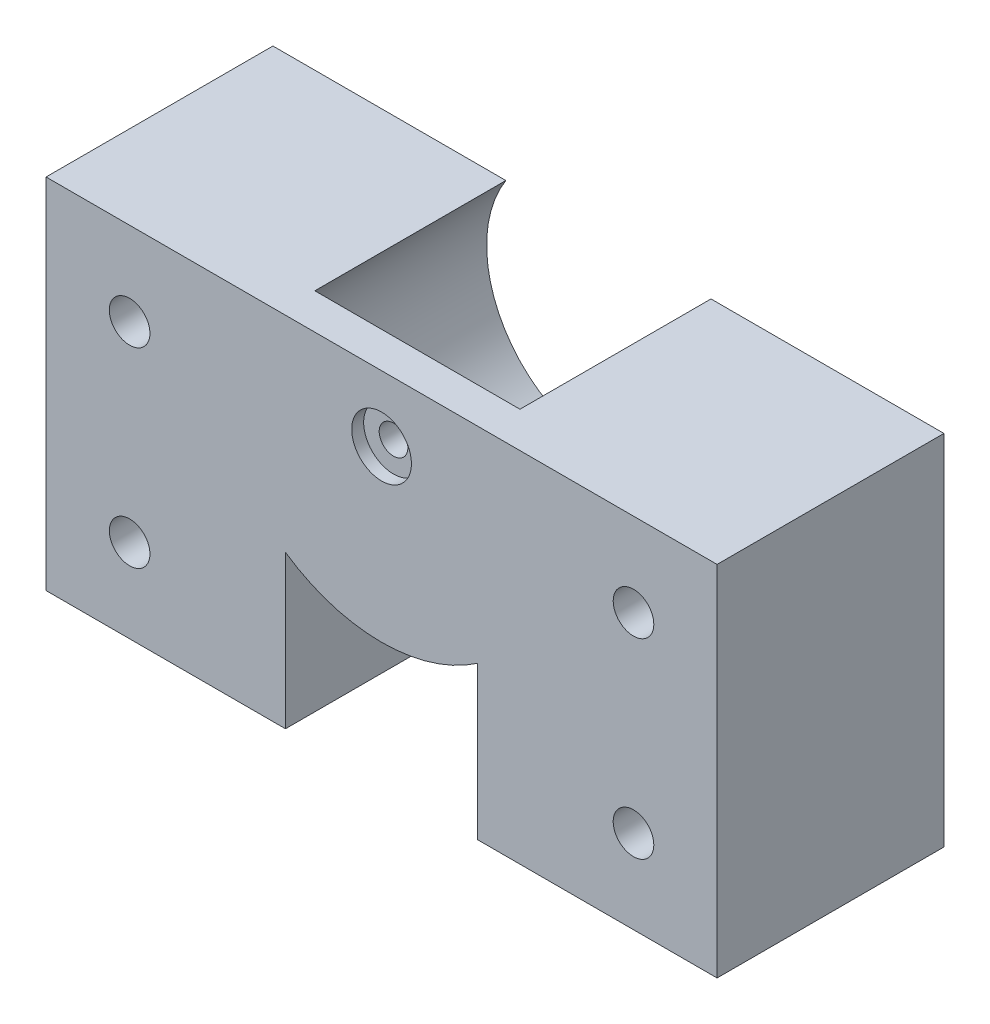
SolidWorks part; units mm, degrees
ref_plane "Front Plane" through (0, 0, 0) normal (0, 0, 1) x (1, 0, 0)
ref_plane "Top Plane" through (0, 0, 0) normal (0, 1, 0) x (1, 0, 0)
ref_plane "Right Plane" through (0, 0, 0) normal (1, 0, 0) x (0, 0, -1)
sketch "Sketch1" plane through (0, 0, 0) normal (0, 0, 1) x (1, 0, 0)
  line L0 (19.5099, 0) -> (0, 0)
  line L1 (28.1, -5.5) -> (28.1, -10) construction
  line L2 (0, 0) -> (0, -30)
  line L3 (0, -30) -> (56.2, -30)
  line L4 (36.6901, 0) -> (56.2, 0)
  line L5 (56.2, 0) -> (56.2, -30)
  line L6 (19.5099, 0) -> (36.6901, 0) construction
  line L7 (35.8259, 0) -> (36.6901, 0)
  line L8 (35.8259, -3) -> (37.9889, -3)
  line L18 (0, -15) -> (56.2, -15) construction
  arc A0 (19.5099, 0) -> (37.9889, -3) centre (28.1, -5.5) ccw
  arc A1 (35.8259, 0) -> (35.8259, -3) centre (35.8259, -1.5) ccw
  dimension "D4" = 30
  dimension "D5" = 1.5
  dimension "D2" = 5.5
  dimension "D1" = 10.2
  dimension "D3" = 56.2
extrude "Boss-Extrude1" add sketch "Sketch1" along normal blind 16
sketch "Sketch2" [suppressed] plane through (0, 0, 0) normal (0, 0, -1) x (-1, 0, 0)
  line L0 (-56.2, -15) -> (0, -15) construction
  line L1 (-56.2, -30) -> (-56.2, 0) construction
  line L2 (-46.0015, -7) -> (-47.6007, -4.23)
  line L3 (-47.6007, -4.23) -> (-50.7993, -4.23)
  line L4 (-50.7993, -4.23) -> (-52.3985, -7)
  line L5 (-52.3985, -7) -> (-50.7993, -9.77)
  line L6 (-50.7993, -9.77) -> (-47.6007, -9.77)
  line L7 (-47.6007, -9.77) -> (-46.0015, -7)
  line L8 (0, 0) -> (0, -30) construction
  line L9 (-8.5993, -9.77) -> (-10.1985, -7)
  line L10 (-28.1, 0) -> (-28.1, -30) construction
  line L11 (0, -30) -> (-56.2, -30) construction
  line L12 (-5.4007, -9.77) -> (-8.5993, -9.77)
  line L13 (-3.8015, -7) -> (-5.4007, -9.77)
  line L14 (-5.4007, -4.23) -> (-3.8015, -7)
  line L15 (-8.5993, -4.23) -> (-5.4007, -4.23)
  line L16 (-10.1985, -7) -> (-8.5993, -4.23)
  line L17 (-10.1985, -23) -> (-8.5993, -25.77)
  line L18 (-8.5993, -25.77) -> (-5.4007, -25.77)
  line L19 (-5.4007, -25.77) -> (-3.8015, -23)
  line L20 (-3.8015, -23) -> (-5.4007, -20.23)
  line L21 (-5.4007, -20.23) -> (-8.5993, -20.23)
  line L22 (-8.5993, -20.23) -> (-10.1985, -23)
  line L23 (-47.6007, -20.23) -> (-46.0015, -23)
  line L24 (-50.7993, -20.23) -> (-47.6007, -20.23)
  line L25 (-52.3985, -23) -> (-50.7993, -20.23)
  line L26 (-50.7993, -25.77) -> (-52.3985, -23)
  line L27 (-47.6007, -25.77) -> (-50.7993, -25.77)
  line L28 (-46.0015, -23) -> (-47.6007, -25.77)
  circle A0 centre (-49.2, -7) radius 2.77 construction
  circle A1 centre (-7, -7) radius 2.77 construction
  circle A2 centre (-7, -23) radius 2.77 construction
  circle A3 centre (-49.2, -23) radius 2.77 construction
  dimension "D1" = 5.54
  dimension "D2" = 7
  dimension "D3" = 7
extrude "Cut-Extrude1" [suppressed] cut sketch "Sketch2" against normal blind 2.4
sketch "Sketch3" plane through (0, 0, 16) normal (0, 0, 1) x (1, 0, 0)
  line L0 (0, 0) -> (0, -30)
  line L1 (0, -30) -> (56.2, -30)
  line L2 (56.2, -30) -> (56.2, 0) construction
  line L3 (56.2, -30) -> (56.2, 0)
  line L4 (0, 0) -> (56.2, 0)
extrude "Boss-Extrude2" add sketch "Sketch3" along normal blind 3
sketch "Sketch4" plane through (0, 0, 0) normal (0, 0, -1) x (-1, 0, 0)
  line L0 (-56.2, -15) -> (0, -15) construction
  line L1 (-56.2, -30) -> (-56.2, 0) construction
  line L2 (0, 0) -> (0, -30) construction
  line L3 (-28.1, -5.5) -> (-28.1, -30) construction
  line L8 (0, -30) -> (-56.2, -30) construction
  circle A0 centre (-49.2, -7) radius 1.7
  circle A1 centre (-7, -7) radius 1.7
  circle A2 centre (-7, -23) radius 1.7
  circle A3 centre (-49.2, -23) radius 1.7
  circle A4 centre (-28.1, -5.5) radius 1.2
  arc A5 (-37.9889, -3) -> (-19.5099, 0) centre (-28.1, -5.5) ccw construction
  dimension "D1" = 3.4
  dimension "D4" = 2.4
  dimension "D2" = 7
  dimension "D3" = 7
extrude "Cut-Extrude2" cut sketch "Sketch4" against normal up to surface (19 mm away) up to face at (28.1, -15, 19)
sketch "Sketch5" plane through (0, 0, 0) normal (0, 0, -1) x (-1, 0, 0)
  line L0 (-19.5099, 0) -> (-36.6901, 0)
  line L1 (-56.2, 0) -> (-35.8259, 0) construction
  arc A0 (-36.6901, 0) -> (-19.5099, 0) centre (-28.1, -5.5) ccw
extrude "Cut-Extrude3" cut sketch "Sketch5" against normal up to surface (16 mm away) up to face at (29.3, -5.5, 16)
sketch "Sketch7" plane through (0, 0, 19) normal (0, 0, 1) x (1, 0, 0)
  line L0 (28.1, -5.5) -> (28.1, -30) construction
  line L1 (22.35, -8) -> (33.85, -8)
  line L2 (22.35, -8) -> (22.35, -13.4)
  line L3 (22.35, -13.4) -> (33.85, -13.4)
  line L4 (33.85, -8) -> (33.85, -13.4)
  line L5 (0, -30) -> (56.2, -30) construction
  circle A0 centre (28.1, -5.5) radius 2
  dimension "D1" = 4
  dimension "D2" = 5.75
  dimension "D3" = 5.4
  dimension "D4" = 8
  dimension "D5" = 5.75
extrude "Cut-Extrude4" [suppressed] cut sketch "Sketch7" against normal blind 2
sketch "Sketch8" plane through (0, 0, 19) normal (0, 0, 1) x (1, 0, 0)
  line L0 (28.1, 0) -> (28.1, -30) construction
  line L1 (56.2, 0) -> (0, 0) construction
  line L2 (0, -30) -> (56.2, -30) construction
  line L3 (0, -15) -> (56.2, -15) construction
  line L4 (0, 0) -> (0, -30) construction
  line L5 (56.2, -30) -> (56.2, 0) construction
  circle A0 centre (7, -7) radius 2.875
  circle A1 centre (49.2, -7) radius 2.875
  circle A2 centre (49.2, -23) radius 2.875
  circle A3 centre (7, -23) radius 2.875
  dimension "D1" = 5.75
extrude "Cut-Extrude5" [suppressed] cut sketch "Sketch8" against normal blind 3
sketch "Sketch9" plane through (0, 0, 0) normal (0, 0, 1) x (1, 0, 0)
  line L0 (23, -30) -> (33.2, -30) construction
  line L1 (0, -30) -> (56.2, -30) construction
  line L2 (33.2, -30) -> (36.15, -30) construction
  line L3 (28.1, -5.5) -> (28.1, -30) construction
  line L4 (36.15, -30) -> (36.15, -17.1978)
  line L5 (36.15, -30) -> (20.05, -30)
  line L6 (23, -30) -> (20.05, -30) construction
  line L7 (20.05, -30) -> (20.05, -17.1978)
  circle A0 centre (28.1, -5.5) radius 14.2 construction
  circle A3 centre (28.1, -5.5) radius 10.2 construction
  arc A4 (20.05, -17.1978) -> (36.15, -17.1978) centre (28.1, -5.5) ccw
  dimension "D1" = 28.4
  dimension "D2" = 20.4
  dimension "D3" = 5.1
  dimension "D4" = 2.95
extrude "Cut-Extrude6" cut sketch "Sketch9" along normal up to next
sketch "Sketch10" plane through (0, 0, 19) normal (0, 0, 1) x (1, 0, 0)
  circle A0 centre (28.1, -5.5) radius 2.5
  dimension "D1" = 5
extrude "Cut-Extrude7" cut sketch "Sketch10" against normal blind 1
